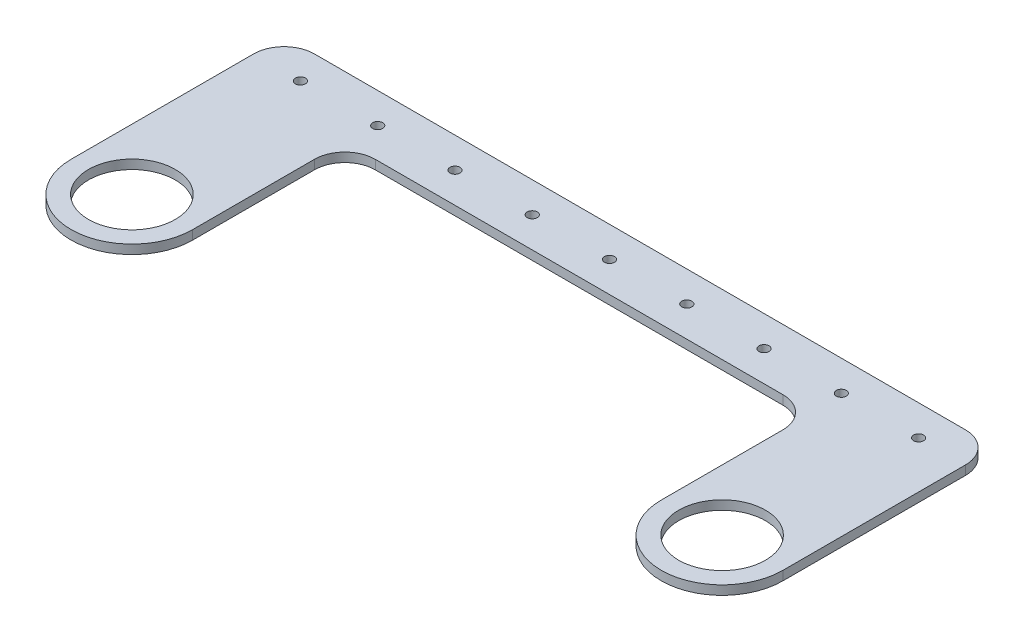
SolidWorks part; units mm, degrees
ref_plane "Front Plane" through (0, 0, 0) normal (0, 0, 1) x (1, 0, 0)
ref_plane "Top Plane" through (0, 0, 0) normal (0, 1, 0) x (1, 0, 0)
ref_plane "Right Plane" through (0, 0, 0) normal (1, 0, 0) x (0, 0, -1)
sketch "Sketch1" plane through (0, 0, 0) normal (0, 1, 0) x (1, 0, 0)
  line L0 (0, 0) -> (0, 18.1373) construction
  line L1 (-117, -10) -> (117, -10)
  line L2 (-117, -10) -> (-117, 10)
  line L3 (-117, 10) -> (117, 10)
  line L4 (117, -10) -> (117, 10)
  line L5 (-117, -10) -> (117, 10) construction
  line L6 (-117, 10) -> (117, -10) construction
  line L7 (-117, 10) -> (-77, 10)
  line L8 (-117, 10) -> (-117, -60)
  line L10 (-77, 10) -> (-77, -60)
  line L11 (117, 10) -> (117, -60)
  line L12 (77, 10) -> (77, -60)
  circle A0 centre (-97, -60) radius 20
  circle A1 centre (-97, -60) radius 14.26
  arc A2 (-57, -10) -> (-77, -30) centre (-57, -30) ccw
  circle A3 centre (97, -60) radius 14.26
  circle A4 centre (97, -60) radius 20
  arc A5 (57, -10) -> (77, -30) centre (57, -30) cw
  circle A6 centre (0, 0) radius 1.65
  circle A7 centre (25.4, 0) radius 1.65
  circle A8 centre (50.8, 0) radius 1.65
  circle A9 centre (76.2, 0) radius 1.65
  circle A10 centre (101.6, 0) radius 1.65
  circle A11 centre (-25.4, 0) radius 1.65
  circle A12 centre (-50.8, 0) radius 1.65
  circle A13 centre (-76.2, 0) radius 1.65
  circle A14 centre (-101.6, 0) radius 1.65
  point P0 (0, 0)
  dimension "D5" = 40
  dimension "D6" = 28.52
  dimension "D7" = 40
  dimension "D3" = 3.3
  dimension "D1" = 20
  dimension "D2" = 234
  dimension "D4" = 40
  dimension "D8" = 5
  dimension "D9" = 5
extrude "Boss-Extrude1" add sketch "Sketch1" along normal blind 3 contours A0 L10 L1 L8 | A0 A1 | L10 L3 L2 L1 | L12 L3 L10 L1 | L3 L12 L1 L4 | L12 A4 L11 L1 | A4 A3
fillet "Fillet1" radius 10 4 edges at (117, 1.5, -10) (-117, 1.5, -10) (77, 1.5, 10) (-77, 1.5, 10)
